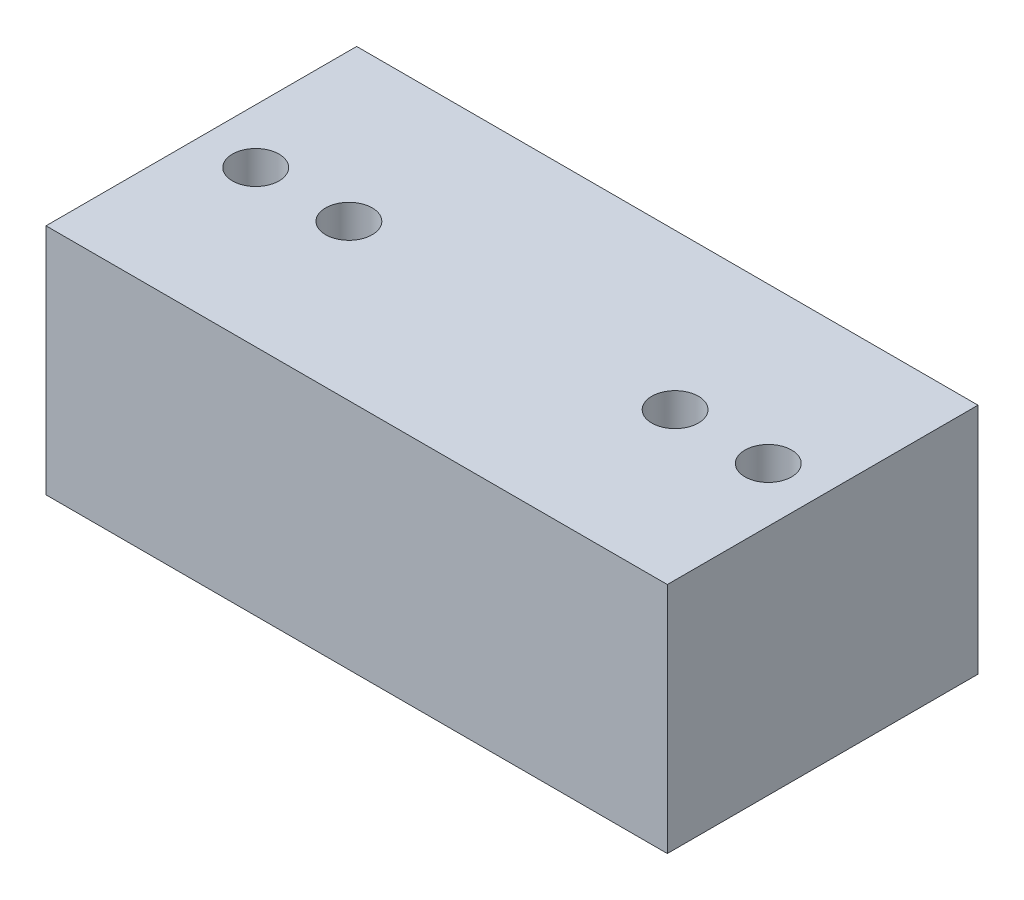
SolidWorks part; units mm, degrees
ref_plane "Front Plane" through (0, 0, 0) normal (0, 0, 1) x (1, 0, 0)
ref_plane "Top Plane" through (0, 0, 0) normal (0, 1, 0) x (1, 0, 0)
ref_plane "Right Plane" through (0, 0, 0) normal (1, 0, 0) x (0, 0, -1)
sketch "Sketch1" plane through (0, 0, 0) normal (0, 1, 0) x (1, 0, 0)
  line L0 (0, 47.3913) -> (0, -58.4986) construction
  line L1 (-40, 31.1005) -> (40, 31.1005)
  line L2 (-40, 31.1005) -> (-40, -8.8995)
  line L3 (-40, -8.8995) -> (40, -8.8995)
  line L4 (40, 31.1005) -> (40, -8.8995)
  circle A0 centre (-33, 11.1005) radius 3
  circle A1 centre (33, 11.1005) radius 3
  point P12 (0, -8.8995)
  point P13 (0, 31.1005)
extrude "Boss-Extrude1" add sketch "Sketch1" along normal blind 30
sketch "Sketch2" plane through (0, 30, 0) normal (0, 1, 0) x (-1, 0, 0)
  circle A0 centre (21, -11.1005) radius 3
  circle A1 centre (-21, -11.1005) radius 3
extrude "Cut-Extrude1" cut sketch "Sketch2" against normal blind 15
cosmetic thread "Cosmetic Thread1" parameters "D2"=7
cosmetic thread "Cosmetic Thread2" parameters "D2"=7
cosmetic thread "Cosmetic Thread3" parameters "D2"=7
sketch "Sketch3"
